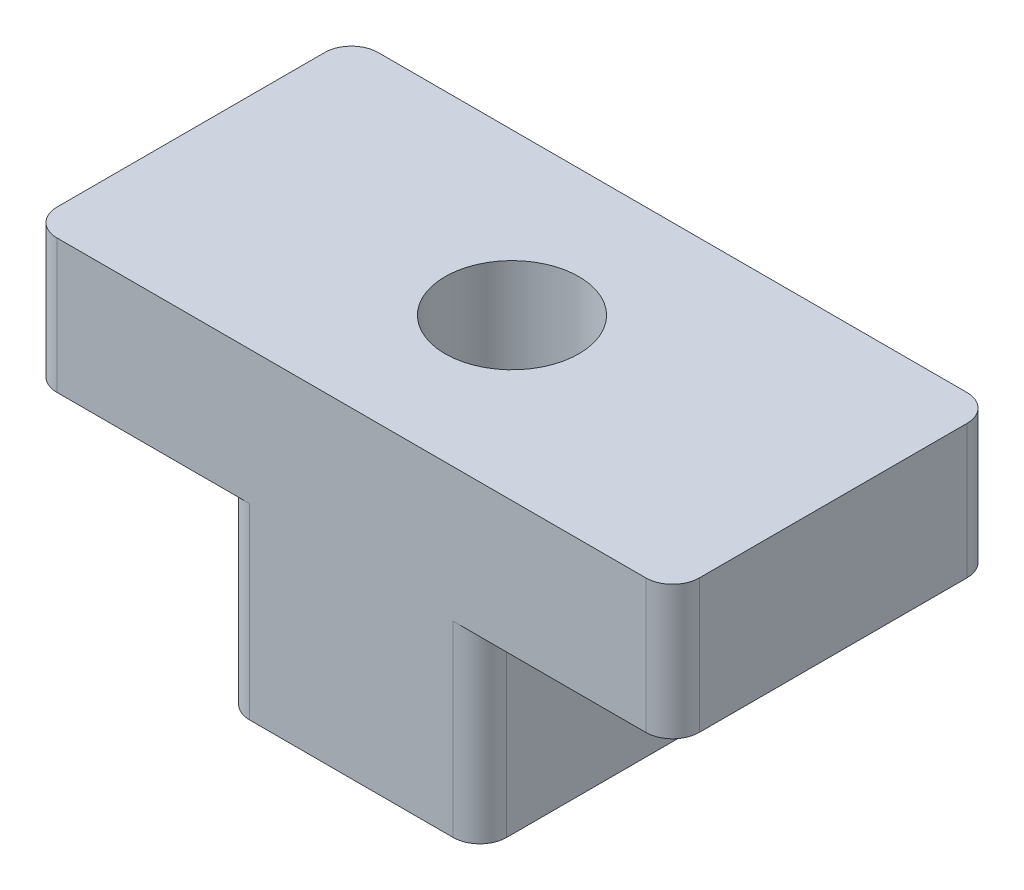
SolidWorks part; units mm, degrees
ref_plane "Plan de face" through (0, 0, 0) normal (0, 0, 1) x (1, 0, 0)
ref_plane "Plan de dessus" through (0, 0, 0) normal (0, 1, 0) x (1, 0, 0)
ref_plane "Plan de droite" through (0, 0, 0) normal (1, 0, 0) x (0, 0, -1)
sketch "Esquisse1" plane through (0, 0, 0) normal (0, 0, 1) x (1, 0, 0)
  line L0 (-6, 0) -> (-2.4, 0)
  line L1 (-2.4, -3.5) -> (2.4, -3.5)
  line L2 (-6, 0) -> (-6, 2.5)
  line L3 (-6, 2.5) -> (6, 2.5)
  line L4 (6, 0) -> (6, 2.5)
  line L5 (-6, 0) -> (6, 0) construction
  line L7 (-2.4, 0) -> (-2.4, -3.5)
  line L8 (6, 0) -> (2.4, 0)
  line L9 (2.4, 0) -> (2.4, -3.5)
  point P0 (0, 0)
  dimension "D1" = 12
  dimension "D2" = 4.8
  dimension "D3" = 2.5
  dimension "D4" = 3.5
extrude "Boss.-Extru.1" add sketch "Esquisse1" along normal mid plane 6
sketch "Esquisse2" plane through (0, 2.5, 0) normal (0, 1, 0) x (1, 0, 0)
  circle A0 centre (0, 0) radius 1.25
  dimension "D1" = 2.5
extrude "Enlèv. mat.-Extru.1" cut sketch "Esquisse2" against normal through all
fillet "Congé2" radius 0.5 8 edges at (-6, 1.25, -3) (-2.4, -1.75, -3) (2.4, -1.75, -3) (6, 1.25, -3) (2.4, -1.75, 3) (-2.4, -1.75, 3) (-6, 1.25, 3) (6, 1.25, 3)
